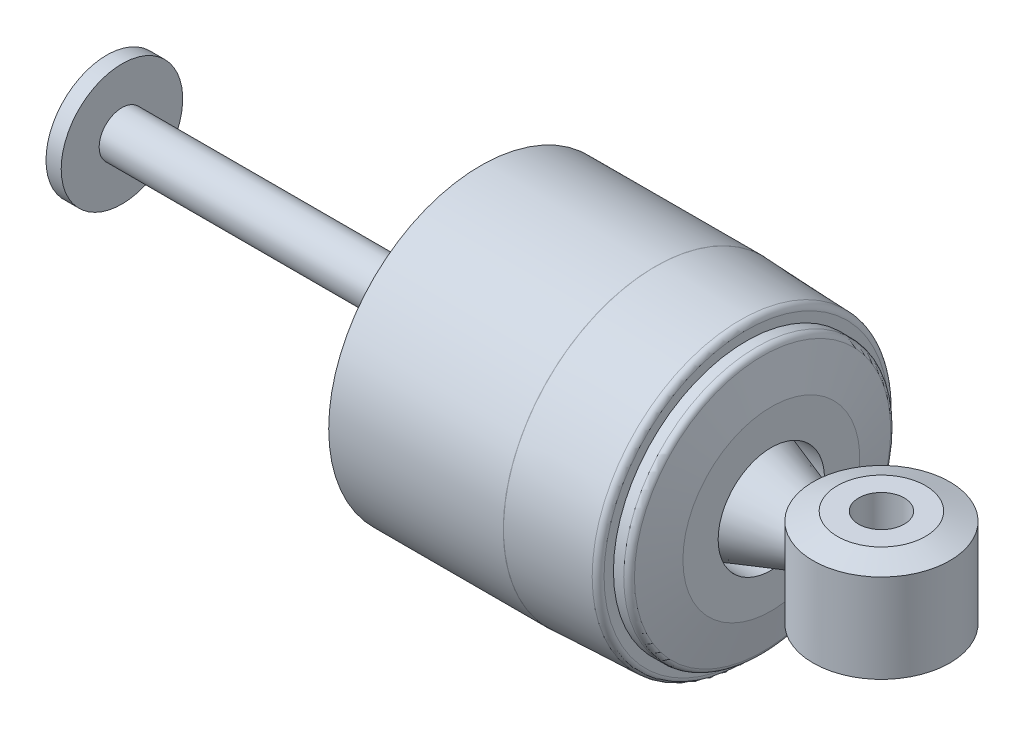
SolidWorks part; units mm, degrees
ref_plane "Front Plane" through (0, 0, 0) normal (0, 0, 1) x (1, 0, 0)
ref_plane "Top Plane" through (0, 0, 0) normal (0, 1, 0) x (1, 0, 0)
ref_plane "Right Plane" through (0, 0, 0) normal (1, 0, 0) x (0, 0, -1)
sketch "Sketch1" plane through (0, 0, 0) normal (0, 1, 0) x (1, 0, 0)
  line L0 (-68.0073, -5.1858) -> (-68.0073, 20.2142)
  line L1 (-68.0073, 20.2142) -> (-64.8323, 20.2142)
  line L2 (-64.8323, 20.2142) -> (-64.8323, 12.2767)
  line L3 (-64.8323, 12.2767) -> (65.3427, 12.2767)
  line L4 (65.3427, 12.2767) -> (65.3427, 18.6267)
  line L5 (65.3427, 18.6267) -> (81.3447, 13.2292)
  line L6 (81.3447, 13.2292) -> (81.3447, 1.7992)
  line L7 (-68.0073, 7.5142) -> (81.3447, 7.5142) construction
  line L8 (65.3427, -3.5983) -> (81.3447, 1.7992)
  line L9 (65.3427, 2.7517) -> (65.3427, -3.5983)
  line L10 (-64.8323, 2.7517) -> (65.3427, 2.7517)
  line L11 (-64.8323, -5.1858) -> (-64.8323, 2.7517)
  line L12 (-68.0073, -5.1858) -> (-64.8323, -5.1858)
  dimension "D1" = 3.175
  dimension "D2" = 130.175
  dimension "D3" = 25.4
  dimension "D4" = 9.525
  dimension "D5" = 11.43
  dimension "D6" = 6.35
  dimension "D7" = 16.002
revolve "Revolve1" add sketch "Sketch1" angle 360 about L7
sketch "Sketch2" plane through (0, 0, 0) normal (0, 1, 0) x (1, 0, 0)
  line L0 (93.9177, 7.5142) -> (81.3447, 7.5142) construction
  line L1 (81.3447, 1.7992) -> (81.3447, 13.2292) construction
  line L2 (65.3427, 18.6267) -> (65.3427, -3.5983) construction
  circle A0 centre (93.9177, 7.5142) radius 14.2875
  circle A1 centre (93.9177, 7.5142) radius 4.7625
  dimension "D1" = 9.525
  dimension "D2" = 28.575
  dimension "D3" = 28.575
extrude "Boss-Extrude1" add sketch "Sketch2" along normal mid plane 22.225 separate body
chamfer "Chamfer1" distance 5.08 angle 20 1 edges at (93.9177, 11.1125, 6.7733)
sketch "Sketch3" plane through (0, 0, 0) normal (0, 1, 0) x (1, 0, 0)
  line L0 (65.3427, 12.2767) -> (65.3427, 18.6267)
  line L1 (65.3427, 18.6267) -> (70.899, 18.6267)
  line L2 (70.899, 18.6267) -> (70.899, 25.9927)
  line L3 (70.899, 25.9927) -> (68.8534, 35.2955)
  line L4 (68.8534, 35.2955) -> (65.6784, 35.2955)
  line L5 (65.6784, 35.2955) -> (65.6784, 38.4705)
  line L6 (65.6784, 38.4705) -> (46.6449, 39.2642)
  line L7 (46.6449, 39.2642) -> (10.1324, 39.2642)
  line L8 (10.1324, 39.2642) -> (10.1324, 38.4705)
  line L9 (10.1324, 38.4705) -> (46.6284, 38.4705)
  line L10 (46.6284, 38.4705) -> (59.9436, 37.9152)
  line L11 (59.9436, 37.9152) -> (64.549, 28.9232)
  line L12 (64.549, 28.9232) -> (64.549, 12.2767)
  line L13 (65.3427, 12.2767) -> (-64.8323, 12.2767) construction
  line L14 (64.549, 12.2767) -> (65.3427, 12.2767)
  line L15 (-68.0867, 7.5142) -> (93.9177, 7.5142) construction
  line L16 (-64.8323, 7.5142) -> (-68.0073, 7.5142) construction
  line L17 (64.549, 2.7517) -> (65.3427, 2.7517)
  line L18 (64.549, -13.8947) -> (64.549, 2.7517)
  line L19 (59.9436, -22.8867) -> (64.549, -13.8947)
  line L20 (46.6284, -23.442) -> (59.9436, -22.8867)
  line L21 (10.1324, -23.442) -> (46.6284, -23.442)
  line L22 (10.1324, -24.2358) -> (10.1324, -23.442)
  line L23 (46.6449, -24.2358) -> (10.1324, -24.2358)
  line L24 (65.6784, -23.442) -> (46.6449, -24.2358)
  line L25 (65.6784, -20.267) -> (65.6784, -23.442)
  line L26 (68.8534, -20.267) -> (65.6784, -20.267)
  line L27 (70.899, -10.9643) -> (68.8534, -20.267)
  line L28 (70.899, -3.5983) -> (70.899, -10.9643)
  line L29 (65.3427, -3.5983) -> (70.899, -3.5983)
  line L30 (65.3427, 2.7517) -> (65.3427, -3.5983)
  dimension "D1" = 0.7937
  dimension "D2" = 63.5
  dimension "D3" = 36.5125
  dimension "D4" = 19.05
  dimension "D5" = 0.7937
  dimension "D6" = 6.35
  dimension "D7" = 0.7937
  dimension "D8" = 3.175
  dimension "D9" = 3.175
  dimension "D10" = 9.525
  dimension "D11" = 7.366
  dimension "D12" = 10.1027
revolve "Revolve2" add sketch "Sketch3" angle 360 about L15
fillet "Fillet1" radius 1.27 3 edges at (46.6449, 0, 24.2358) (65.6784, 0, 23.442) (68.8534, 0, 20.267)
